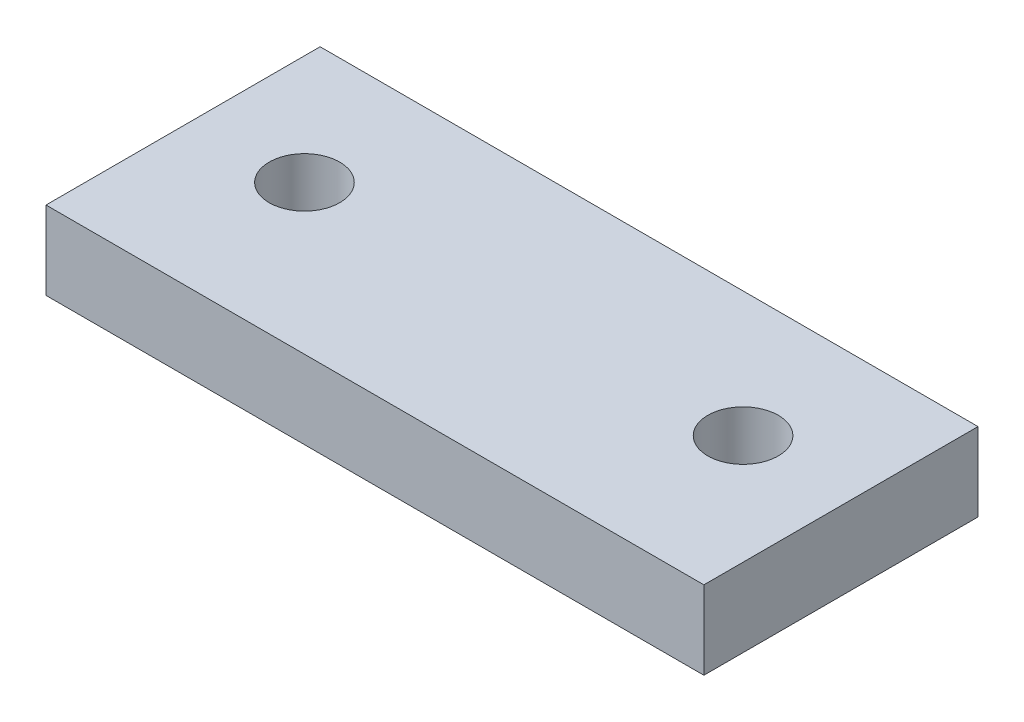
SolidWorks part; units mm, degrees
ref_plane "Front Plane" through (0, 0, 0) normal (0, 0, 1) x (1, 0, 0)
ref_plane "Top Plane" through (0, 0, 0) normal (0, 1, 0) x (1, 0, 0)
ref_plane "Right Plane" through (0, 0, 0) normal (1, 0, 0) x (0, 0, -1)
sketch "Sketch1" plane through (0, 0, 0) normal (0, 1, 0) x (1, 0, 0)
  line L1 (0, 0) -> (42, 0)
  line L2 (0, 0) -> (0, 17.5)
  line L3 (0, 17.5) -> (42, 17.5)
  line L4 (42, 0) -> (42, 17.5)
  dimension "D1" = 42
  dimension "D2" = 17.5
extrude "Boss-Extrude1" add sketch "Sketch1" along normal blind 5
sketch "Sketch2" plane through (0, 5, 0) normal (0, 1, 0) x (1, 0, 0)
  line L1 (21, 17.5) -> (21, 0) construction
  line L2 (42, 17.5) -> (0, 17.5) construction
  line L3 (0, 0) -> (42, 0) construction
  circle A0 centre (7, 9.5) radius 2.25
  circle A1 centre (35, 9.5) radius 2.25
  dimension "D1" = 4.5
  dimension "D2" = 9.5
  dimension "D3" = 14
extrude "Cut-Extrude1" cut sketch "Sketch2" against normal through all
